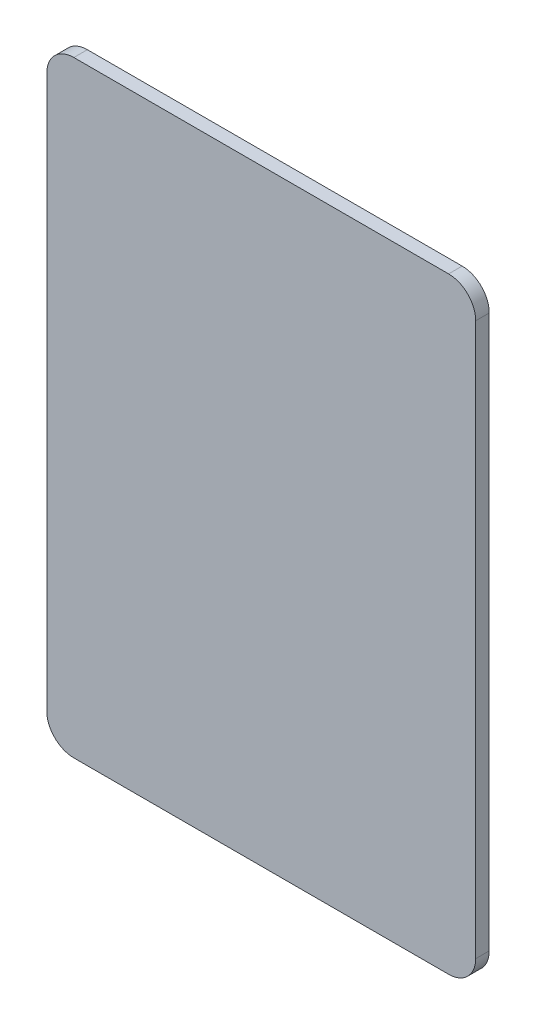
SolidWorks part; units mm, degrees
ref_plane "Front Plane" through (0, 0, 0) normal (0, 0, 1) x (1, 0, 0)
ref_plane "Top Plane" through (0, 0, 0) normal (0, 1, 0) x (1, 0, 0)
ref_plane "Right Plane" through (0, 0, 0) normal (1, 0, 0) x (0, 0, -1)
sketch "Sketch1" plane through (0, 0, 0) normal (0, 0, 1) x (1, 0, 0)
  line L1 (0, 0) -> (50.292, 0)
  line L2 (0, 0) -> (0, 71.12)
  line L3 (0, 71.12) -> (50.292, 71.12)
  line L4 (50.292, 0) -> (50.292, 71.12)
  dimension "D1" = 71.12
  dimension "D2" = 50.292
extrude "Boss-Extrude1" add sketch "Sketch1" along normal blind 1.5875
fillet "Fillet1" radius 3.175 4 edges at (50.292, 0, 0.7937) (0, 0, 0.7937) (0, 71.12, 0.7937) (50.292, 71.12, 0.7937)
